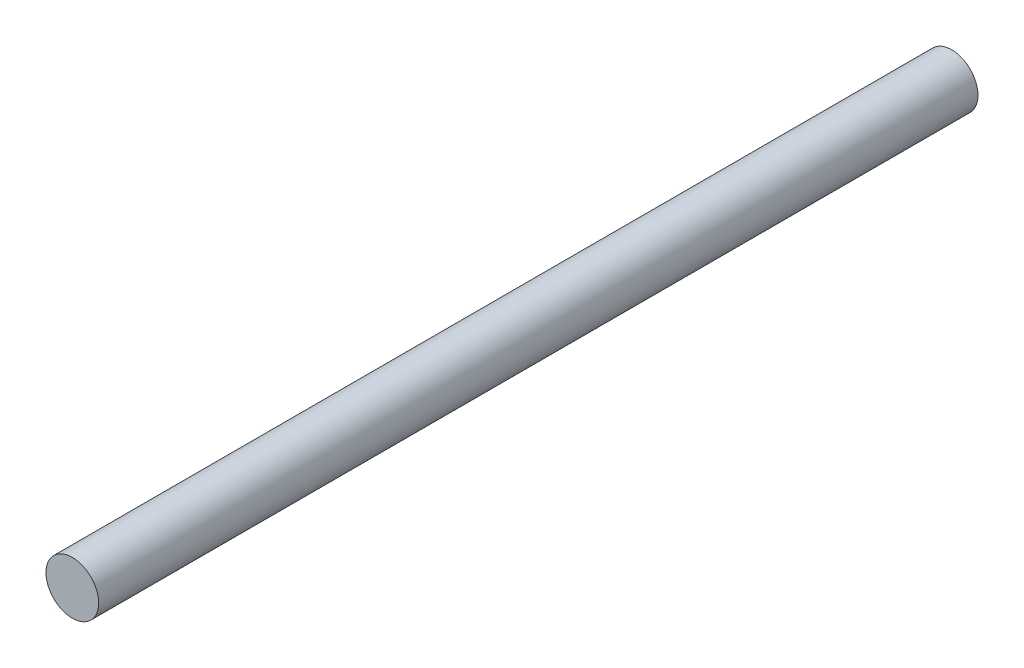
SolidWorks part; units mm, degrees
ref_plane "Front Plane" through (0, 0, 0) normal (0, 0, 1) x (1, 0, 0)
ref_plane "Top Plane" through (0, 0, 0) normal (0, 1, 0) x (1, 0, 0)
ref_plane "Right Plane" through (0, 0, 0) normal (1, 0, 0) x (0, 0, -1)
sketch "Sketch1" plane through (0, 0, 0) normal (0, 0, 1) x (1, 0, 0)
  circle A0 centre (0, 0) radius 4.5
  dimension "D1" = 9
extrude "Boss-Extrude1" add sketch "Sketch1" along normal blind 150
sketch "Sketch2" plane through (0, 0, 150) normal (0, 0, 1) x (1, 0, 0)
  point P0 (0, 0)
sketch "Sketch3" plane through (0, 0, 0) normal (0, 0, -1) x (-1, 0, 0)
  point P0 (0, 0)
